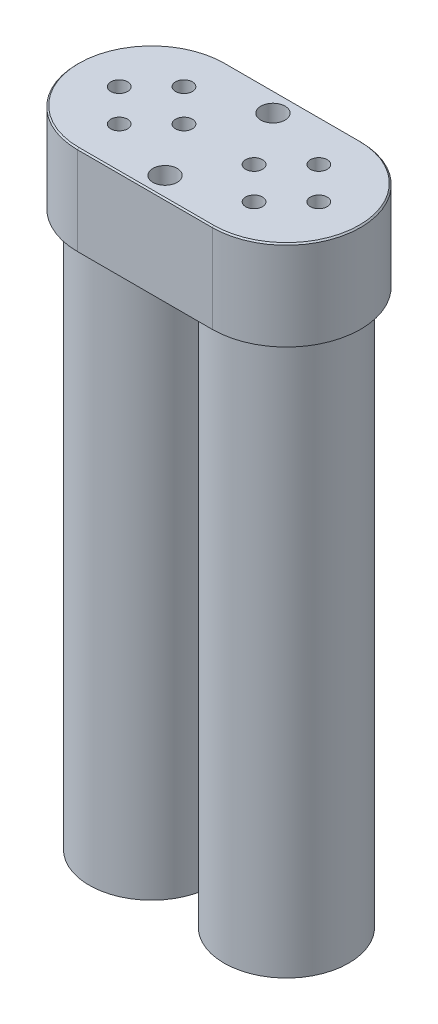
SolidWorks part; units mm, degrees
ref_plane "Front Plane" through (0, 0, 0) normal (0, 0, 1) x (1, 0, 0)
ref_plane "Top Plane" through (0, 0, 0) normal (0, 1, 0) x (1, 0, 0)
ref_plane "Right Plane" through (0, 0, 0) normal (1, 0, 0) x (0, 0, -1)
sketch "Sketch1" plane through (0, 0, 0) normal (0, 1, 0) x (1, 0, 0)
  line L0 (0, 0) -> (25.4, 0) construction
  line L1 (0, 13.97) -> (25.4, 13.97)
  line L2 (0, -13.97) -> (25.4, -13.97)
  arc A0 (0, 13.97) -> (0, -13.97) centre (0, 0) ccw
  arc A1 (25.4, -13.97) -> (25.4, 13.97) centre (25.4, 0) ccw
  point P3 (12.7, 0)
  dimension "D1" = 27.94
  dimension "D2" = 25.4
extrude "Boss-Extrude1" add sketch "Sketch1" along normal blind 16.8656
chamfer "Chamfer1" distance 0.254 angle 45 4 edges at (39.37, 16.8656, 0) (12.7, 16.8656, -13.97) (12.7, 16.8656, 13.97) (-13.97, 16.8656, 0)
sketch "Sketch2" plane through (0, 0, 0) normal (0, -1, 0) x (1, 0, 0)
  circle A4 centre (0, 0) radius 11.7475
  circle A5 centre (25.4, 0) radius 11.7475
extrude "Boss-Extrude2" add sketch "Sketch2" along normal blind 104.521
sketch "Sketch3" plane through (0, 16.8656, 0) normal (0, 1, 0) x (1, 0, 0)
  line L0 (12.7, 13.716) -> (12.7, -13.716) construction
  line L1 (25.4, 13.716) -> (0, 13.716) construction
  line L2 (0, -13.716) -> (25.4, -13.716) construction
  circle A0 centre (25.4, 0) radius 6.096 construction
  circle A1 centre (25.4, 6.096) radius 1.5875
  circle A2 centre (31.496, 0) radius 1.5875
  circle A3 centre (25.4, -6.096) radius 1.5875
  circle A4 centre (19.304, 0) radius 1.5875
  circle A5 centre (-6.096, 0) radius 1.5875
  circle A6 centre (0, 0) radius 6.096 construction
  circle A7 centre (6.096, 0) radius 1.5875
  circle A8 centre (0, -6.096) radius 1.5875
  circle A9 centre (0, 6.096) radius 1.5875
  dimension "D1" = 12.192
  dimension "D2" = 3.175
extrude "Cut-Extrude1" cut sketch "Sketch3" against normal blind 16.3576
sketch "Sketch4" plane through (0, 16.8656, 0) normal (0, 1, 0) x (1, 0, 0)
  line L0 (0, 13.97) -> (25.4, 13.97) construction
  line L1 (-12.2403, 0) -> (39.116, 0) construction
  circle A1 centre (12.7, 10.16) radius 2.286
  arc A2 (25.4, -13.716) -> (25.4, 13.716) centre (25.4, 0) ccw construction
  circle A3 centre (12.7, -10.16) radius 2.286
  dimension "D1" = 3.81
extrude "Cut-Extrude2" cut sketch "Sketch4" against normal through all
ref_plane "Plane1" through (12.7, 0, 0) normal (1, 0, 0) x (0, 0, -1)
